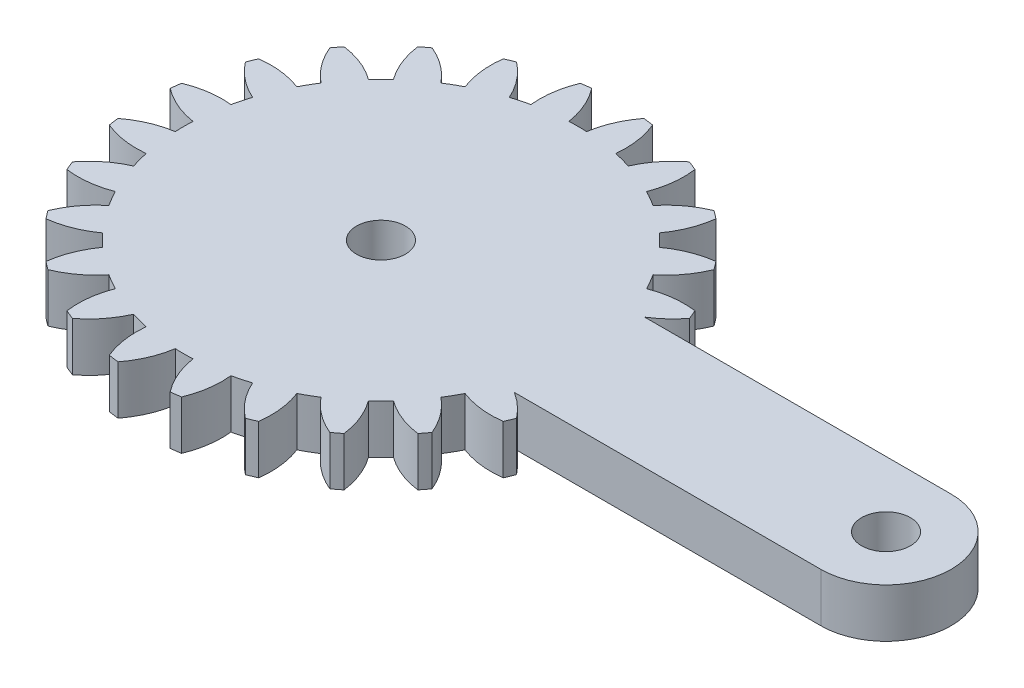
SolidWorks part; units mm, degrees
ref_plane "Front Plane" through (0, 0, 0) normal (0, 0, 1) x (1, 0, 0)
ref_plane "Top Plane" through (0, 0, 0) normal (0, 1, 0) x (1, 0, 0)
ref_plane "Right Plane" through (0, 0, 0) normal (1, 0, 0) x (0, 0, -1)
sketch "Sketch1" plane through (0, 0, 0) normal (0, 1, 0) x (1, 0, 0)
  line L0 (12.188, -4) -> (31, -4)
  line L1 (31, 4) -> (12.188, 4)
  line L2 (0, 0) -> (31, 0) construction
  line L3 (0, 0) -> (0, 19.1149) construction
  circle A2 centre (31, 0) radius 1.5
  arc A3 (13.6281, -5.3071) -> (12.188, -4) centre (9.3381, -8.5867) ccw
  arc A4 (13.3892, -5.8838) -> (13.6281, -5.3071) centre (0, 0) ccw
  arc A5 (10.7334, -5.5703) -> (13.3892, -5.8838) centre (12.6747, -0.5313) ccw
  arc A6 (10.1907, -6.5103) -> (10.7334, -5.5703) centre (0, 0) ccw
  arc A7 (11.7901, -8.6535) -> (10.1907, -6.5103) centre (6.7975, -10.711) ccw
  arc A8 (11.4102, -9.1487) -> (11.7901, -8.6535) centre (0, 0) ccw
  arc A9 (8.926, -8.1585) -> (11.4102, -9.1487) centre (12.1053, -3.7936) ccw
  arc A10 (8.1585, -8.926) -> (8.926, -8.1585) centre (0, 0) ccw
  arc A11 (9.1487, -11.4102) -> (8.1585, -8.926) centre (3.7936, -12.1053) ccw
  arc A12 (8.6535, -11.7901) -> (9.1487, -11.4102) centre (0, 0) ccw
  arc A13 (6.5103, -10.1907) -> (8.6535, -11.7901) centre (10.711, -6.7975) ccw
  arc A14 (5.5703, -10.7334) -> (6.5103, -10.1907) centre (0, 0) ccw
  arc A15 (5.8838, -13.3892) -> (5.5703, -10.7334) centre (0.5313, -12.6747) ccw
  arc A16 (5.3071, -13.6281) -> (5.8838, -13.3892) centre (0, 0) ccw
  arc A17 (3.6509, -11.5285) -> (5.3071, -13.6281) centre (8.5867, -9.3381) ccw
  arc A18 (2.6025, -11.8094) -> (3.6509, -11.5285) centre (0, 0) ccw
  arc A19 (2.2179, -14.4558) -> (2.6025, -11.8094) centre (-2.7673, -12.3803) ccw
  arc A20 (1.5991, -14.5373) -> (2.2179, -14.4558) centre (0, 0) ccw
  arc A21 (0.5427, -12.0806) -> (1.5991, -14.5373) centre (5.8773, -11.2423) ccw
  arc A22 (-0.5427, -12.0806) -> (0.5427, -12.0806) centre (0, 0) ccw
  arc A23 (-1.5991, -14.5373) -> (-0.5427, -12.0806) centre (-5.8773, -11.2423) ccw
  arc A24 (-2.2179, -14.4558) -> (-1.5991, -14.5373) centre (0, 0) ccw
  arc A25 (-2.6025, -11.8094) -> (-2.2179, -14.4558) centre (2.7673, -12.3803) ccw
  arc A26 (-3.6509, -11.5285) -> (-2.6025, -11.8094) centre (0, 0) ccw
  arc A27 (-5.3071, -13.6281) -> (-3.6509, -11.5285) centre (-8.5867, -9.3381) ccw
  arc A28 (-5.8838, -13.3892) -> (-5.3071, -13.6281) centre (0, 0) ccw
  arc A29 (-5.5703, -10.7334) -> (-5.8838, -13.3892) centre (-0.5313, -12.6747) ccw
  arc A30 (-6.5103, -10.1907) -> (-5.5703, -10.7334) centre (0, 0) ccw
  arc A31 (-8.6535, -11.7901) -> (-6.5103, -10.1907) centre (-10.711, -6.7975) ccw
  arc A32 (-9.1487, -11.4102) -> (-8.6535, -11.7901) centre (0, 0) ccw
  arc A33 (-8.1585, -8.926) -> (-9.1487, -11.4102) centre (-3.7936, -12.1053) ccw
  arc A34 (-8.926, -8.1585) -> (-8.1585, -8.926) centre (0, 0) ccw
  arc A35 (-11.4102, -9.1487) -> (-8.926, -8.1585) centre (-12.1053, -3.7936) ccw
  arc A36 (-11.7901, -8.6535) -> (-11.4102, -9.1487) centre (0, 0) ccw
  arc A37 (-10.1907, -6.5103) -> (-11.7901, -8.6535) centre (-6.7975, -10.711) ccw
  arc A38 (-10.7334, -5.5703) -> (-10.1907, -6.5103) centre (0, 0) ccw
  arc A39 (-13.3892, -5.8838) -> (-10.7334, -5.5703) centre (-12.6747, -0.5313) ccw
  arc A40 (-13.6281, -5.3071) -> (-13.3892, -5.8838) centre (0, 0) ccw
  arc A41 (-11.5285, -3.6509) -> (-13.6281, -5.3071) centre (-9.3381, -8.5867) ccw
  arc A42 (-11.8094, -2.6025) -> (-11.5285, -3.6509) centre (0, 0) ccw
  arc A43 (-14.4558, -2.2179) -> (-11.8094, -2.6025) centre (-12.3803, 2.7673) ccw
  arc A44 (-14.5373, -1.5991) -> (-14.4558, -2.2179) centre (0, 0) ccw
  arc A45 (-12.0806, -0.5427) -> (-14.5373, -1.5991) centre (-11.2423, -5.8773) ccw
  arc A46 (-12.0806, 0.5427) -> (-12.0806, -0.5427) centre (0, 0) ccw
  arc A47 (-14.5373, 1.5991) -> (-12.0806, 0.5427) centre (-11.2423, 5.8773) ccw
  arc A48 (-14.4558, 2.2179) -> (-14.5373, 1.5991) centre (0, 0) ccw
  arc A49 (-11.8094, 2.6025) -> (-14.4558, 2.2179) centre (-12.3803, -2.7673) ccw
  arc A50 (-11.5285, 3.6509) -> (-11.8094, 2.6025) centre (0, 0) ccw
  arc A51 (-13.6281, 5.3071) -> (-11.5285, 3.6509) centre (-9.3381, 8.5867) ccw
  arc A52 (-13.3892, 5.8838) -> (-13.6281, 5.3071) centre (0, 0) ccw
  arc A53 (-10.7334, 5.5703) -> (-13.3892, 5.8838) centre (-12.6747, 0.5313) ccw
  arc A54 (-10.1907, 6.5103) -> (-10.7334, 5.5703) centre (0, 0) ccw
  arc A55 (-11.7901, 8.6535) -> (-10.1907, 6.5103) centre (-6.7975, 10.711) ccw
  arc A56 (-11.4102, 9.1487) -> (-11.7901, 8.6535) centre (0, 0) ccw
  arc A57 (-8.926, 8.1585) -> (-11.4102, 9.1487) centre (-12.1053, 3.7936) ccw
  arc A58 (-8.1585, 8.926) -> (-8.926, 8.1585) centre (0, 0) ccw
  arc A59 (-9.1487, 11.4102) -> (-8.1585, 8.926) centre (-3.7936, 12.1053) ccw
  arc A60 (-8.6535, 11.7901) -> (-9.1487, 11.4102) centre (0, 0) ccw
  arc A61 (-6.5103, 10.1907) -> (-8.6535, 11.7901) centre (-10.711, 6.7975) ccw
  arc A62 (-5.5703, 10.7334) -> (-6.5103, 10.1907) centre (0, 0) ccw
  arc A63 (-5.8838, 13.3892) -> (-5.5703, 10.7334) centre (-0.5313, 12.6747) ccw
  arc A64 (-5.3071, 13.6281) -> (-5.8838, 13.3892) centre (0, 0) ccw
  arc A65 (-3.6509, 11.5285) -> (-5.3071, 13.6281) centre (-8.5867, 9.3381) ccw
  arc A66 (-2.6025, 11.8094) -> (-3.6509, 11.5285) centre (0, 0) ccw
  arc A67 (-2.2179, 14.4558) -> (-2.6025, 11.8094) centre (2.7673, 12.3803) ccw
  arc A68 (-1.5991, 14.5373) -> (-2.2179, 14.4558) centre (0, 0) ccw
  arc A69 (-0.5427, 12.0806) -> (-1.5991, 14.5373) centre (-5.8773, 11.2423) ccw
  arc A70 (0.5427, 12.0806) -> (-0.5427, 12.0806) centre (0, 0) ccw
  arc A71 (1.5991, 14.5373) -> (0.5427, 12.0806) centre (5.8773, 11.2423) ccw
  arc A72 (2.2179, 14.4558) -> (1.5991, 14.5373) centre (0, 0) ccw
  arc A73 (2.6025, 11.8094) -> (2.2179, 14.4558) centre (-2.7673, 12.3803) ccw
  arc A74 (3.6509, 11.5285) -> (2.6025, 11.8094) centre (0, 0) ccw
  arc A75 (5.3071, 13.6281) -> (3.6509, 11.5285) centre (8.5867, 9.3381) ccw
  arc A76 (5.8838, 13.3892) -> (5.3071, 13.6281) centre (0, 0) ccw
  arc A77 (5.5703, 10.7334) -> (5.8838, 13.3892) centre (0.5313, 12.6747) ccw
  arc A78 (6.5103, 10.1907) -> (5.5703, 10.7334) centre (0, 0) ccw
  arc A79 (8.6535, 11.7901) -> (6.5103, 10.1907) centre (10.711, 6.7975) ccw
  arc A80 (9.1487, 11.4102) -> (8.6535, 11.7901) centre (0, 0) ccw
  arc A81 (8.1585, 8.926) -> (9.1487, 11.4102) centre (3.7936, 12.1053) ccw
  arc A82 (8.926, 8.1585) -> (8.1585, 8.926) centre (0, 0) ccw
  arc A83 (11.4102, 9.1487) -> (8.926, 8.1585) centre (12.1053, 3.7936) ccw
  arc A84 (11.7901, 8.6535) -> (11.4102, 9.1487) centre (0, 0) ccw
  arc A85 (10.1907, 6.5103) -> (11.7901, 8.6535) centre (6.7975, 10.711) ccw
  arc A86 (10.7334, 5.5703) -> (10.1907, 6.5103) centre (0, 0) ccw
  arc A87 (13.3892, 5.8838) -> (10.7334, 5.5703) centre (12.6747, 0.5313) ccw
  arc A88 (13.6281, 5.3071) -> (13.3892, 5.8838) centre (0, 0) ccw
  arc A89 (12.188, 4) -> (13.6281, 5.3071) centre (9.3381, 8.5867) ccw
  arc A90 (31, -4) -> (31, 4) centre (31, 0) ccw
  circle A91 centre (0, 0) radius 1.5
  point P2 (0, 0)
  point P139 (0, 0)
  point P140 (-39.6054, 11.4431)
  dimension "D1" = 3
  dimension "D2" = 12.0927
  dimension "D4" = 4
  dimension "D5" = 3
  dimension "D7" = 14.625
  dimension "D8" = 5.4
  dimension "D9" = 5.4
  dimension "D3" = 31
  dimension "D6" = 18.812
extrude "Boss-Extrude2" add sketch "Sketch1" along normal blind 3
